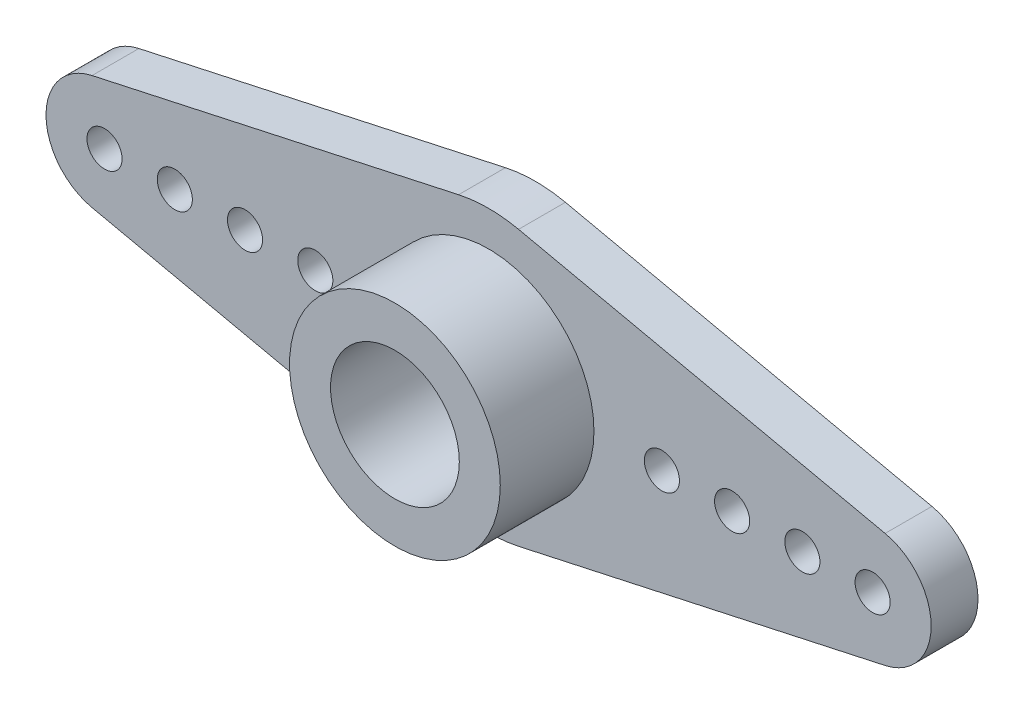
SolidWorks part; units mm, degrees
ref_plane "Ön Düzlem" through (0, 0, 0) normal (0, 0, 1) x (1, 0, 0)
ref_plane "Üst Düzlem" through (0, 0, 0) normal (0, 1, 0) x (1, 0, 0)
ref_plane "Sağ Düzlem" through (0, 0, 0) normal (1, 0, 0) x (0, 0, -1)
sketch "Çizim1" plane through (0, 0, 0) normal (0, 0, 1) x (1, 0, 0)
  line L0 (-16.9335, 2.4424) -> (-1.2805, 5.8618)
  line L1 (-16.9335, -2.4424) -> (-1.2805, -5.8618)
  line L2 (16.9335, -2.4424) -> (1.2805, -5.8618)
  line L3 (16.9335, 2.4424) -> (1.2805, 5.8618)
  circle A0 centre (0, 0) radius 1.5
  arc A1 (1.2805, 5.8618) -> (-1.2805, 5.8618) centre (0, 0) ccw
  circle A2 centre (7.4, 0) radius 0.75
  circle A3 centre (10.4, 0) radius 0.75
  circle A4 centre (13.4, 0) radius 0.75
  circle A5 centre (16.4, 0) radius 0.75
  circle A6 centre (-7.4, 0) radius 0.75
  circle A7 centre (-10.4, 0) radius 0.75
  circle A8 centre (-13.4, 0) radius 0.75
  circle A9 centre (-16.4, 0) radius 0.75
  arc A11 (16.9335, -2.4424) -> (16.9335, 2.4424) centre (16.4, 0) ccw
  arc A12 (-16.9335, 2.4424) -> (-16.9335, -2.4424) centre (-16.4, 0) ccw
  arc A13 (-1.2805, -5.8618) -> (1.2805, -5.8618) centre (0, 0) ccw
  dimension "D1" = 1.5
  dimension "D10" = 3
  dimension "D11" = 12
  dimension "D12" = 2.5
  dimension "D13" = 2.5
  dimension "D2" = 7.4
  dimension "D3" = 3
  dimension "D4" = 3
  dimension "D5" = 3
  dimension "D6" = 7.4
  dimension "D7" = 3
  dimension "D8" = 3
  dimension "D9" = 3
extrude "Yükseklik-Ekstrüzyon1" add sketch "Çizim1" along normal blind 2
sketch "Çizim2" plane through (0, 0, 2) normal (0, 0, 1) x (1, 0, 0)
  circle A0 centre (0, 0) radius 2.75
  circle A1 centre (0, 0) radius 4.5
  dimension "D1" = 5.5
  dimension "D2" = 9
extrude "Yükseklik-Ekstrüzyon2" add sketch "Çizim2" along normal blind 4
